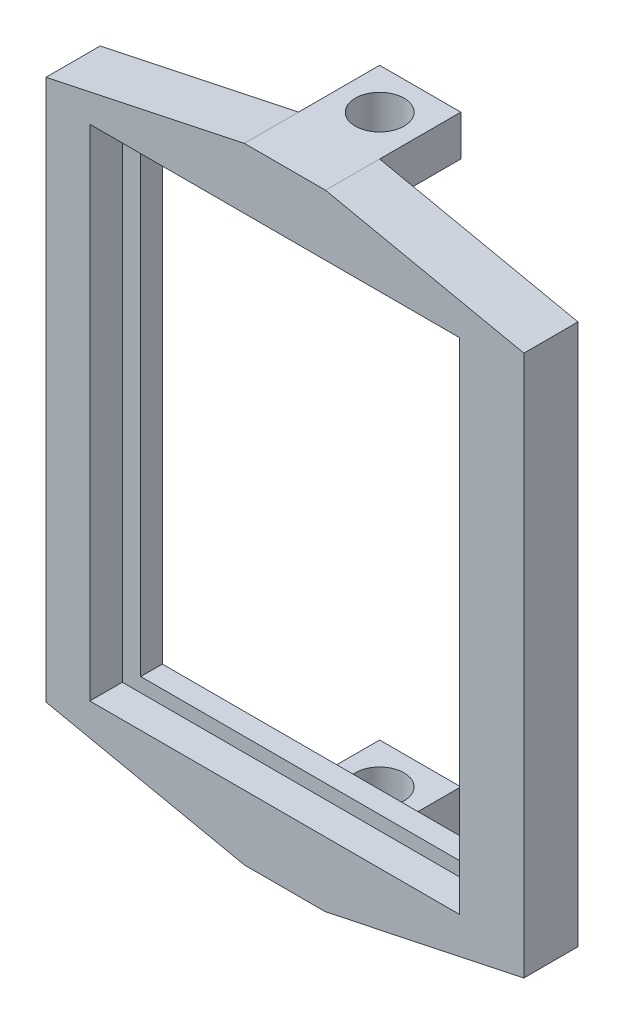
SolidWorks part; units mm, degrees
ref_plane "Plan de face" through (0, 0, 0) normal (0, 0, 1) x (1, 0, 0)
ref_plane "Plan de dessus" through (0, 0, 0) normal (0, 1, 0) x (1, 0, 0)
ref_plane "Plan de droite" through (0, 0, 0) normal (1, 0, 0) x (0, 0, -1)
sketch "Esquisse1" plane through (0, 0, 0) normal (0, 0, 1) x (1, 0, 0)
  line L0 (-30.0581, 26.6932) -> (43.7219, 26.6932) construction
  line L1 (-30.0581, -27.7268) -> (43.7219, -27.9824) construction
  line L7 (10.5819, 28.3482) -> (3.0819, 28.3482)
  line L8 (10.5819, 28.3482) -> (10.5819, 24.5982)
  line L9 (10.5819, 24.5982) -> (3.0819, 24.5982)
  line L10 (3.0819, 28.3482) -> (3.0819, 24.5982)
  line L13 (3.0819, -29.3896) -> (10.5819, -29.3896)
  line L14 (3.0819, -29.3896) -> (3.0819, -25.6396)
  line L15 (3.0819, -25.6396) -> (10.5819, -25.6396)
  line L16 (10.5819, -29.3896) -> (10.5819, -25.6396)
  dimension "D1" = 3.75
  dimension "D2" = 7.5
  dimension "D3" = 7.5
  dimension "D4" = 3.75
extrude "Boss.-Extru.1" add sketch "Esquisse1" along normal blind 7.5 contours L9 L10 L7 L8 | L15 L16 L13 L14
sketch "Esquisse2" plane through (0, 28.3482, 0) normal (0, 1, 0) x (1, 0, 0)
  line L0 (3.0819, 0) -> (10.5819, -7.5) construction
  circle A0 centre (6.8319, -3.75) radius 2.25
  dimension "D1" = 4.5
extrude "Enlèv. mat.-Extru.1" cut sketch "Esquisse2" against normal through all
sketch "Esquisse4" plane through (0, 0, 7.5) normal (0, 0, 1) x (1, 0, 0)
  line L8 (-15.2431, 24.4782) -> (-15.2431, -25.5218)
  line L9 (-10.2431, 22.5532) -> (23.9069, 22.5532) construction
  line L10 (-10.2431, 22.5532) -> (-10.2431, -23.5968) construction
  line L11 (-10.2431, -23.5968) -> (23.9069, -23.5968) construction
  line L12 (23.9069, 22.5532) -> (23.9069, -23.5968) construction
  line L13 (3.0819, 28.3482) -> (10.5819, 28.3482)
  line L14 (-15.2431, 24.4782) -> (3.0819, 28.3482)
  line L15 (6.8319, 28.3482) -> (6.8319, -29.3896) construction
  line L16 (10.5819, 28.3482) -> (28.9069, 24.4782)
  line L17 (-15.2431, -25.5218) -> (3.0819, -29.3896)
  line L18 (3.0819, -29.3896) -> (10.5819, -29.3896)
  line L19 (10.5819, -29.3896) -> (28.9069, -25.5218)
  line L20 (28.9069, 24.4782) -> (28.9069, -25.5218)
  line L27 (22.2069, 21.2482) -> (22.2069, -22.1018)
  line L28 (22.2069, 21.2482) -> (-9.4931, 21.2482)
  line L29 (-9.4931, 21.2482) -> (-9.4931, -22.1018)
  line L30 (22.2069, -22.1018) -> (-9.4931, -22.1018)
  point P5 (-15.2431, -0.5218)
  point P6 (-10.2431, -0.5218)
  dimension "D1" = 50
  dimension "D2" = 0
  dimension "D3" = 34.15
  dimension "D4" = 46.15
  dimension "D5" = 5
extrude "Boss.-Extru.2" add sketch "Esquisse4" along normal blind 2
sketch "Esquisse5" plane through (0, 0, 9.5) normal (0, 0, 1) x (1, 0, 0)
  line L0 (-15.2431, 24.4782) -> (3.0819, 28.3482)
  line L1 (3.0819, 28.3482) -> (10.5819, 28.3482)
  line L2 (10.5819, 28.3482) -> (28.9069, 24.4782)
  line L3 (28.9069, 24.4782) -> (28.9069, -25.5218)
  line L4 (28.9069, -25.5218) -> (10.5819, -29.3896)
  line L5 (10.5819, -29.3896) -> (3.0819, -29.3896)
  line L6 (3.0819, -29.3896) -> (-15.2431, -25.5218)
  line L7 (-15.2431, -25.5218) -> (-15.2431, 24.4782)
  line L8 (-11.1931, -23.4068) -> (-11.1931, 22.7432)
  line L9 (-11.1931, -23.4068) -> (22.9569, -23.4068)
  line L10 (22.9569, -23.4068) -> (22.9569, 22.7432)
  line L11 (-11.1931, 22.7432) -> (22.9569, 22.7432)
  point P24 (22.2069, -22.1018)
extrude "Boss.-Extru.3" add sketch "Esquisse5" along normal blind 3
